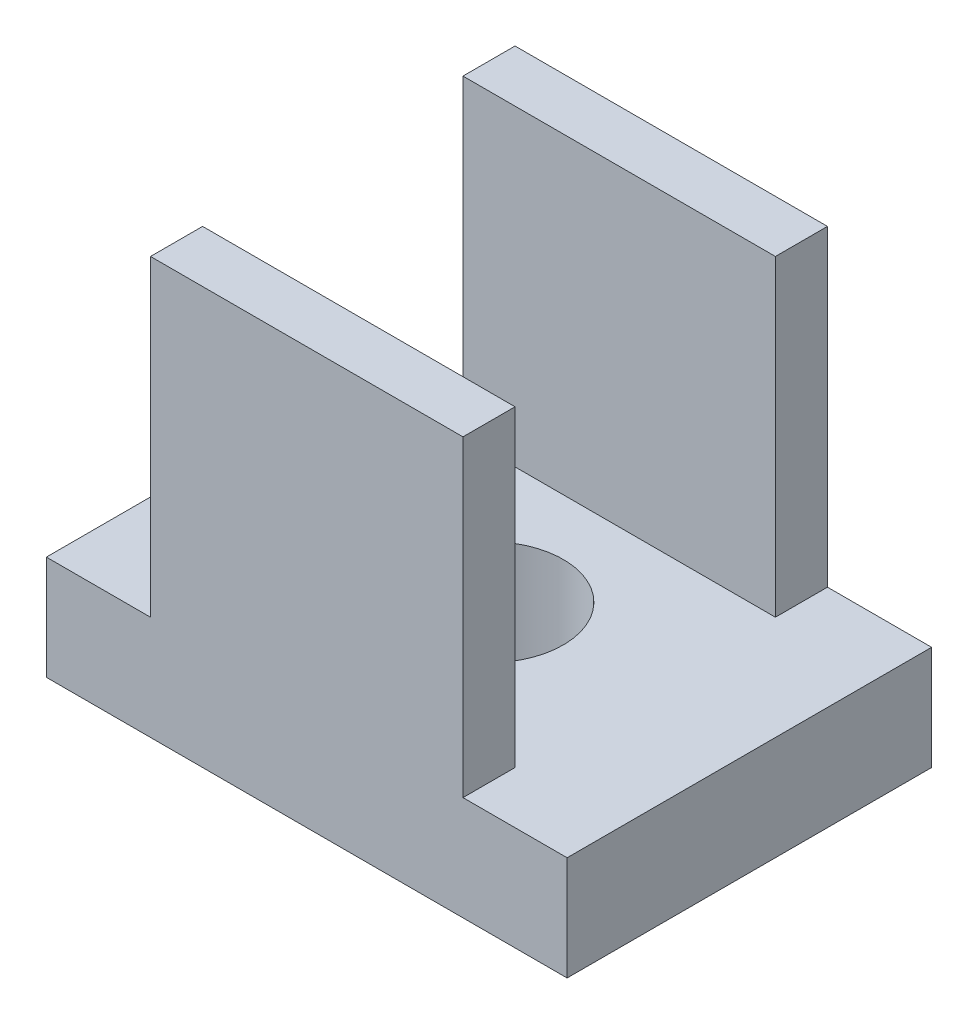
SolidWorks part; units mm, degrees
ref_plane "Front Plane" through (0, 0, 0) normal (0, 0, 1) x (1, 0, 0)
ref_plane "Top Plane" through (0, 0, 0) normal (0, 1, 0) x (1, 0, 0)
ref_plane "Right Plane" through (0, 0, 0) normal (1, 0, 0) x (0, 0, -1)
sketch "Sketch1" plane through (0, 0, 0) normal (0, 1, 0) x (1, 0, 0)
  line L1 (5, -3.5) -> (-5, -3.5)
  line L2 (5, -3.5) -> (5, 3.5)
  line L3 (5, 3.5) -> (-5, 3.5)
  line L4 (-5, -3.5) -> (-5, 3.5)
  line L5 (5, -3.5) -> (-5, 3.5) construction
  line L6 (5, 3.5) -> (-5, -3.5) construction
  point P0 (0, 0)
  dimension "D1" = 10
  dimension "D2" = 7
extrude "Boss-Extrude1" add sketch "Sketch1" along normal blind 2
sketch "Sketch2" plane through (0, 2, 0) normal (0, 1, 0) x (1, 0, 0)
  circle A0 centre (0, 0) radius 1.425
  dimension "D1" = 2.85
extrude "Cut-Extrude1" cut sketch "Sketch2" against normal through all
sketch "Sketch3" plane through (0, 2, 0) normal (0, 1, 0) x (1, 0, 0)
  line L0 (0, 0) -> (0, 2.5) construction
  line L1 (3, 2.5) -> (-3, 2.5)
  line L2 (3, 2.5) -> (3, 3.5)
  line L3 (3, 3.5) -> (-3, 3.5)
  line L4 (-3, 2.5) -> (-3, 3.5)
  line L5 (3, 2.5) -> (-3, 3.5) construction
  line L6 (3, 3.5) -> (-3, 2.5) construction
  line L7 (5, 3.5) -> (-5, 3.5) construction
  point P0 (0, 3)
  dimension "D1" = 6
  dimension "D2" = 1
extrude "Boss-Extrude2" add sketch "Sketch3" along normal blind 6
mirror "Mirror1" about plane through (0, 0, 0) normal (0, 0, 1) of "Boss-Extrude2"
